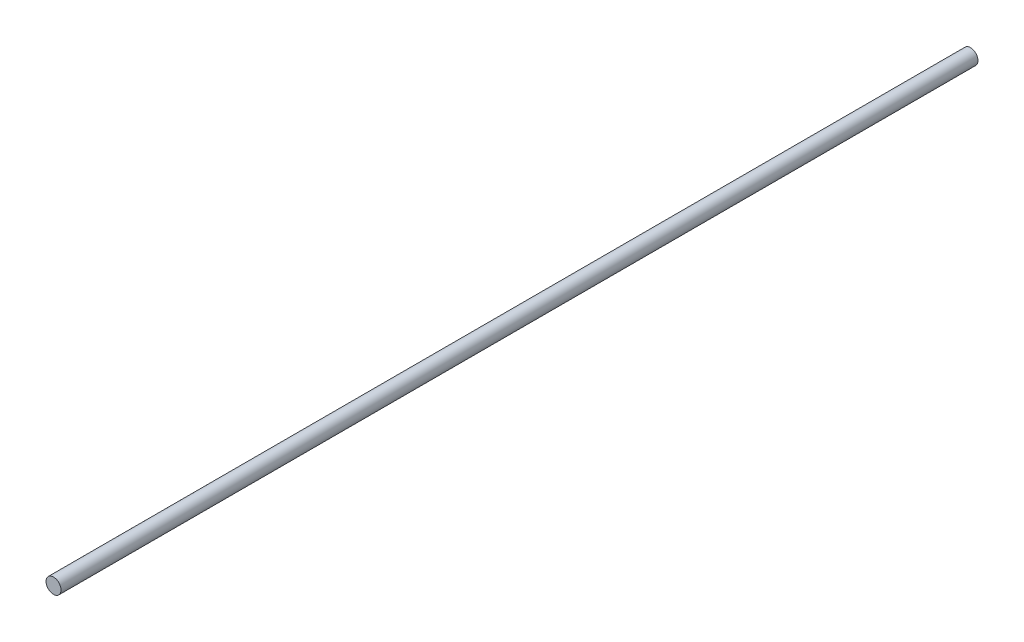
SolidWorks part; units mm, degrees
ref_plane "Front Plane" through (0, 0, 0) normal (0, 0, 1) x (1, 0, 0)
ref_plane "Top Plane" through (0, 0, 0) normal (0, 1, 0) x (1, 0, 0)
ref_plane "Right Plane" through (0, 0, 0) normal (1, 0, 0) x (0, 0, -1)
sketch "Sketch1" plane through (0, 0, 0) normal (0, 0, 1) x (1, 0, 0)
  line L1 (-2.5, 0) -> (2.5, 0) construction
  dimension "OD" = 5
sketch "Sketch2" plane through (0, 0, 0) normal (1, 0, 0) x (0, 0, -1)
  line L0 (152.4, 0) -> (-152.4, 0)
  point P4 (0, 0)
  dimension "Length" = 304.8
sketch "Sketch3" plane through (0, 0, 0) normal (0, 0, 1) x (1, 0, 0)
  circle A0 centre (0, 0) radius 2.5
extrude "Boss-Extrude1" add sketch "Sketch3" along normal up to vertex (152.4 mm away) and the other way up to vertex (152.4 mm away) up to point (0, 0, 152.4) other way up to point (0, 0, -152.4)
